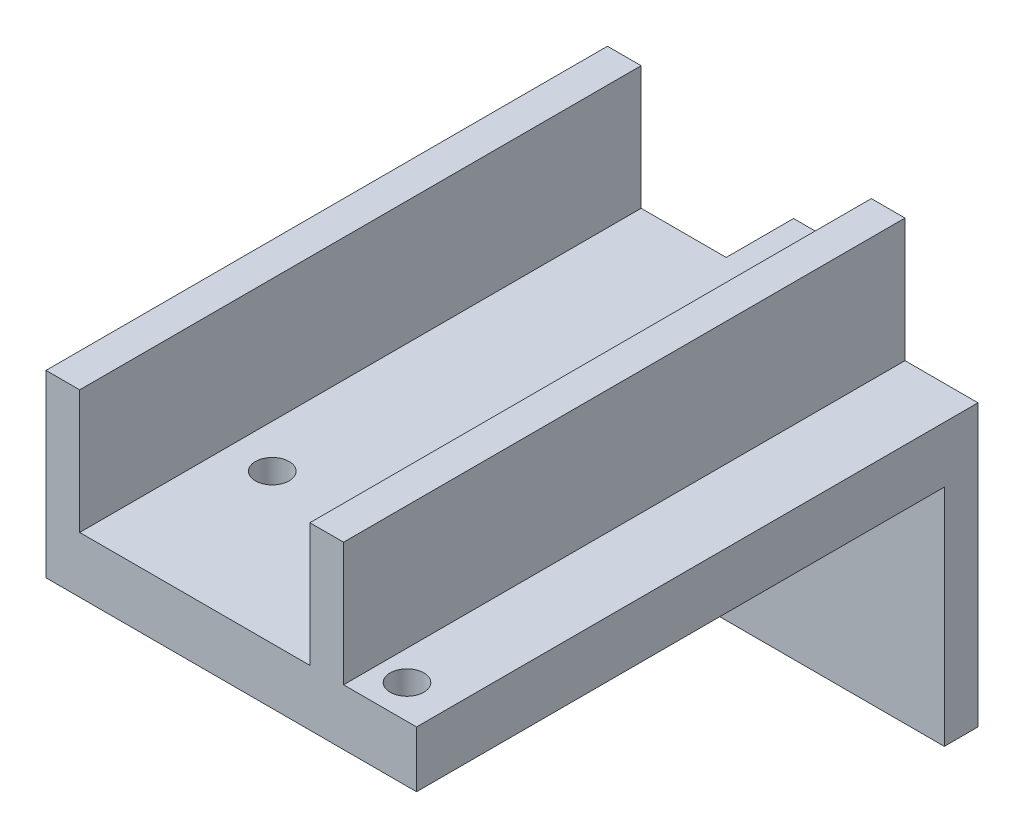
SolidWorks part; units mm, degrees
ref_plane "정면" through (0, 0, 0) normal (0, 0, 1) x (1, 0, 0)
ref_plane "윗면" through (0, 0, 0) normal (0, 1, 0) x (1, 0, 0)
ref_plane "우측면" through (0, 0, 0) normal (1, 0, 0) x (0, 0, -1)
sketch "스케치1" plane through (0, 0, 0) normal (0, 1, 0) x (1, 0, 0)
  line L1 (-15, 25) -> (15, 25)
  line L2 (-15, 25) -> (-15, -25)
  line L3 (-15, -25) -> (15, -25)
  line L4 (15, 25) -> (15, -25)
  line L5 (-15, 25) -> (15, -25) construction
  line L6 (-15, -25) -> (15, 25) construction
  point P4 (0, 0)
  point P5 (0, 0)
  dimension "D1" = 30
  dimension "D2" = 50
extrude "보스-돌출1" add sketch "스케치1" along normal blind 5
sketch "스케치2" plane through (0, 0, 0) normal (0, 1, 0) x (1, 0, 0)
  line L0 (-15, -25) -> (15, -25) construction
  line L1 (-14.15, -8.7) -> (14.15, -8.7) construction
  line L2 (-14.15, -8.7) -> (-14.15, -25) construction
  line L3 (-14.15, -25) -> (14.15, -25) construction
  line L4 (14.15, -8.7) -> (14.15, -25) construction
  line L5 (-14.15, -8.7) -> (14.15, -25) construction
  line L6 (-14.15, -25) -> (14.15, -8.7) construction
  line L7 (-15, 0) -> (15, 0) construction
  line L8 (-15, 25) -> (-15, -25) construction
  line L9 (15, -25) -> (15, 25) construction
  circle A0 centre (-11.15, -11.7) radius 1.5
  circle A1 centre (11.15, -22) radius 1.5
  point P4 (0, -16.85)
  point P5 (0, 0)
  dimension "D3" = 3
  dimension "D4" = 3
  dimension "D5" = 3
  dimension "D6" = 3
  dimension "D7" = 3
  dimension "D1" = 16.3
  dimension "D2" = 28.3
extrude "컷-돌출2" cut sketch "스케치2" against normal blind 3 and the other way through all
sketch "스케치3" plane through (0, 0, -25) normal (0, 0, -1) x (-1, 0, 0)
  line L0 (-15, 5) -> (-15, 0) construction
  line L1 (15, 5) -> (-15, 5)
  line L2 (15, 5) -> (15, -20)
  line L3 (15, -20) -> (-15, -20)
  line L4 (-15, 5) -> (-15, -20)
  line L5 (15, 5) -> (-15, -20) construction
  line L6 (15, -20) -> (-15, 5) construction
  point P4 (0, -7.5)
  dimension "D1" = 25
extrude "보스-돌출2" add sketch "스케치3" against normal blind 3
sketch "스케치4" plane through (0, 0, -25) normal (0, 0, -1) x (-1, 0, 0)
  line L1 (15, 5) -> (-5, 5) construction
  line L2 (15, 5) -> (15, -15) construction
  line L3 (15, -15) -> (-5, -15) construction
  line L4 (-5, 5) -> (-5, -15) construction
  line L5 (15, 5) -> (-5, -15) construction
  line L6 (15, -15) -> (-5, 5) construction
  line L7 (2.575, 5) -> (7.425, 5)
  line L8 (2.575, 5) -> (2.575, -15)
  line L9 (2.575, -15) -> (7.425, -15)
  line L10 (7.425, 5) -> (7.425, -15)
  line L11 (2.575, 5) -> (7.425, -15) construction
  line L12 (2.575, -15) -> (7.425, 5) construction
  point P4 (5, -5)
  point P6 (0, 0)
  point P11 (5, -5)
  point P12 (5, 5)
  dimension "D1" = 4.85
  dimension "D2" = 20
  dimension "D3" = 20
extrude "보스-돌출3" add sketch "스케치4" along normal blind 6 contours L8 L9 L10 L7
sketch "스케치6" plane through (0, 0, 25) normal (0, 0, 1) x (1, 0, 0)
  line L0 (-15, 0) -> (15, 0) construction
  line L1 (-15, 0) -> (-18, 0)
  line L2 (-15, 0) -> (-15, 16)
  line L3 (-15, 16) -> (-18, 16)
  line L4 (-18, 0) -> (-18, 16)
  line L5 (-15, 0) -> (-18, 16) construction
  line L6 (-15, 16) -> (-18, 0) construction
  line L7 (5.5, 0) -> (8.5, 0)
  line L8 (5.5, 0) -> (5.5, 16)
  line L9 (5.5, 16) -> (8.5, 16)
  line L10 (8.5, 0) -> (8.5, 16)
  line L11 (5.5, 0) -> (8.5, 16) construction
  line L12 (5.5, 16) -> (8.5, 0) construction
  point P4 (-16.5, 8)
  point P10 (7, 8)
  dimension "D1" = 20.5
  dimension "D2" = 16
  dimension "D3" = 3
extrude "보스-돌출4" add sketch "스케치6" against normal up to vertex
